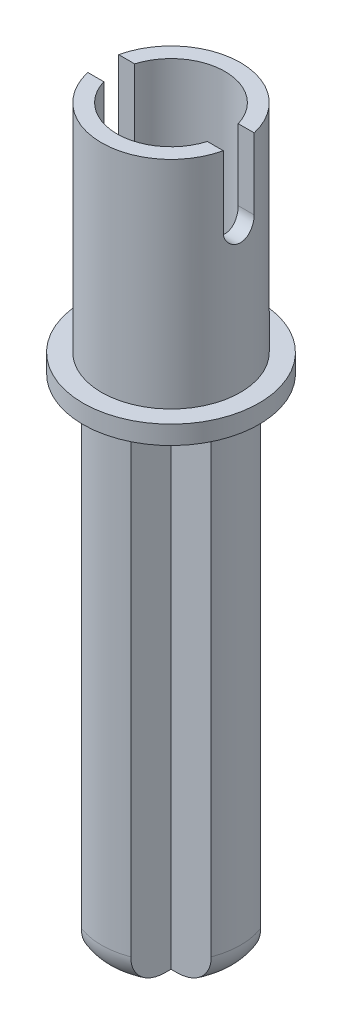
SolidWorks part; units mm, degrees
ref_plane "Front Plane" through (0, 0, 0) normal (0, 0, 1) x (1, 0, 0)
ref_plane "Top Plane" through (0, 0, 0) normal (0, 1, 0) x (1, 0, 0)
ref_plane "Right Plane" through (0, 0, 0) normal (1, 0, 0) x (0, 0, -1)
sketch "Sketch1" plane through (0, 0, 0) normal (0, 1, 0) x (1, 0, 0)
  line L0 (-0.8, -0.8) -> (-0.8, -2.103)
  line L1 (-0.8, 0.8) -> (-2.103, 0.8)
  line L2 (2.103, 0.8) -> (0.8, 0.8)
  line L3 (2.103, -0.8) -> (0.8, -0.8)
  line L4 (0.8, -0.8) -> (0.8, -2.103)
  line L5 (-0.8, -0.8) -> (-2.103, -0.8)
  line L6 (-7.75, 0) -> (-7.75, 0)
  line L7 (-7.75, 0) -> (-7.75, 0)
  line L8 (-0.8, 2.103) -> (-0.8, 0.8)
  line L9 (0.8, 2.103) -> (0.8, 0.8)
  line L10 (-7.75, 0) -> (-7.75, 0)
  line L11 (7.75, 0) -> (7.75, 0)
  line L12 (7.75, 0) -> (7.75, 0)
  line L13 (7.75, 0) -> (7.75, 0)
  line L14 (7.75, 0) -> (7.75, 0)
  line L15 (-7.75, 0) -> (-7.75, 0)
  line L16 (-8.6621, 8.6621) -> (-8.6621, 8.6621)
  line L17 (-8.6621, -8.6621) -> (-8.6621, -8.6621)
  line L18 (-8.6621, -8.6621) -> (-8.6621, -8.6621)
  line L19 (8.6621, -8.6621) -> (8.6621, -8.6621)
  line L20 (8.6621, -8.6621) -> (8.6621, -8.6621)
  line L21 (8.6621, 8.6621) -> (8.6621, 8.6621)
  line L22 (8.6621, 8.6621) -> (8.6621, 8.6621)
  line L23 (-8.6621, 8.6621) -> (-8.6621, 8.6621)
  arc A0 (-2.103, 0.8) -> (-2.103, -0.8) centre (0, 0) ccw
  arc A1 (0.8, 2.103) -> (-0.8, 2.103) centre (0, 0) ccw
  arc A2 (2.103, -0.8) -> (2.103, 0.8) centre (0, 0) ccw
  arc A3 (-0.8, -2.103) -> (0.8, -2.103) centre (0, 0) ccw
  arc A4 (-7.75, 0) -> (-7.75, 0) centre (-7.75, 0) ccw
  arc A5 (-7.75, 0) -> (7.75, 0) centre (0, 0) ccw
  arc A6 (7.75, 0) -> (7.75, 0) centre (7.75, 0) ccw
  arc A7 (7.75, 0) -> (-7.75, 0) centre (0, 0) ccw
  arc A8 (-8.6621, 8.6621) -> (-8.6621, -8.6621) centre (0, 0) ccw
  arc A9 (-8.6621, -8.6621) -> (8.6621, -8.6621) centre (0, 0) ccw
  arc A10 (8.6621, -8.6621) -> (8.6621, 8.6621) centre (0, 0) ccw
  arc A11 (8.6621, 8.6621) -> (-8.6621, 8.6621) centre (0, 0) ccw
  point P26 (0.8, 0)
  dimension "D1" = 4.5
  dimension "D2" = 10
  dimension "D3" = 10
extrude "Boss-Extrude1" add sketch "Sketch1" along normal offset from surface (16.5 mm away) 16.5 contours L0 A3 L4 L3 A2 L2 L9 A1 L8 L1 A0 L5 up to plane "Top Plane"
fillet "Fillet1" radius 1 1 edges at (-2.25, 0, 0)
fillet "Fillet2" radius 1 1 edges at (0, 0, 2.25)
fillet "Fillet3" radius 1 1 edges at (2.25, 0, 0)
fillet "Fillet4" radius 1 1 edges at (0, 0, -2.25)
sketch "Sketch3" plane through (0, 16.5, 0) normal (0, 1, 0) x (1, 0, 0)
  circle A0 centre (0, 0) radius 2.85
  dimension "D1" = 5.7
extrude "Boss-Extrude2" add sketch "Sketch3" against normal blind 0.6 contours A0
sketch "Sketch4" plane through (0, 16.5, 0) normal (0, 1, 0) x (1, 0, 0)
  circle A0 centre (0, 0) radius 2.25
  dimension "D1" = 4.5
extrude "Boss-Extrude3" add sketch "Sketch4" along normal blind 7 contours A0
ref_plane "Plane1" through (10, 0, 0) normal (1, 0, 0) x (0, 0, -1)
sketch "Sketch5" plane through (10, 0, 0) normal (1, 0, 0) x (0, 0, -1)
  line L0 (0, 16.5) -> (0, 21.2) construction
  line L1 (2.85, 16.5) -> (-2.85, 16.5) construction
  line L2 (0, 21.2) -> (0, 23.5) construction
  line L3 (2.25, 23.5) -> (-2.25, 23.5) construction
  line L4 (-0.5, 21.2) -> (-0.5, 23.5)
  line L5 (0.5, 21.2) -> (0.5, 23.5)
  arc A0 (-0.5, 21.2) -> (0.5, 21.2) centre (0, 21.2) ccw
  arc A1 (0.5, 23.5) -> (-0.5, 23.5) centre (0, 23.5) ccw
  point P5 (0, 22.35)
  dimension "D1" = 4.7
extrude "Cut-Extrude2" cut sketch "Sketch5" against normal through all
ref_plane "Plane3" through (0, 23.5, 0) normal (0, 1, 0) x (1, 0, 0)
sketch "Sketch8" plane through (0, 23.5, 0) normal (0, 1, 0) x (1, 0, 0)
  circle A0 centre (0, 0) radius 1.75
  dimension "D1" = 3.5
extrude "Cut-Extrude3" cut sketch "Sketch8" against normal blind 7
